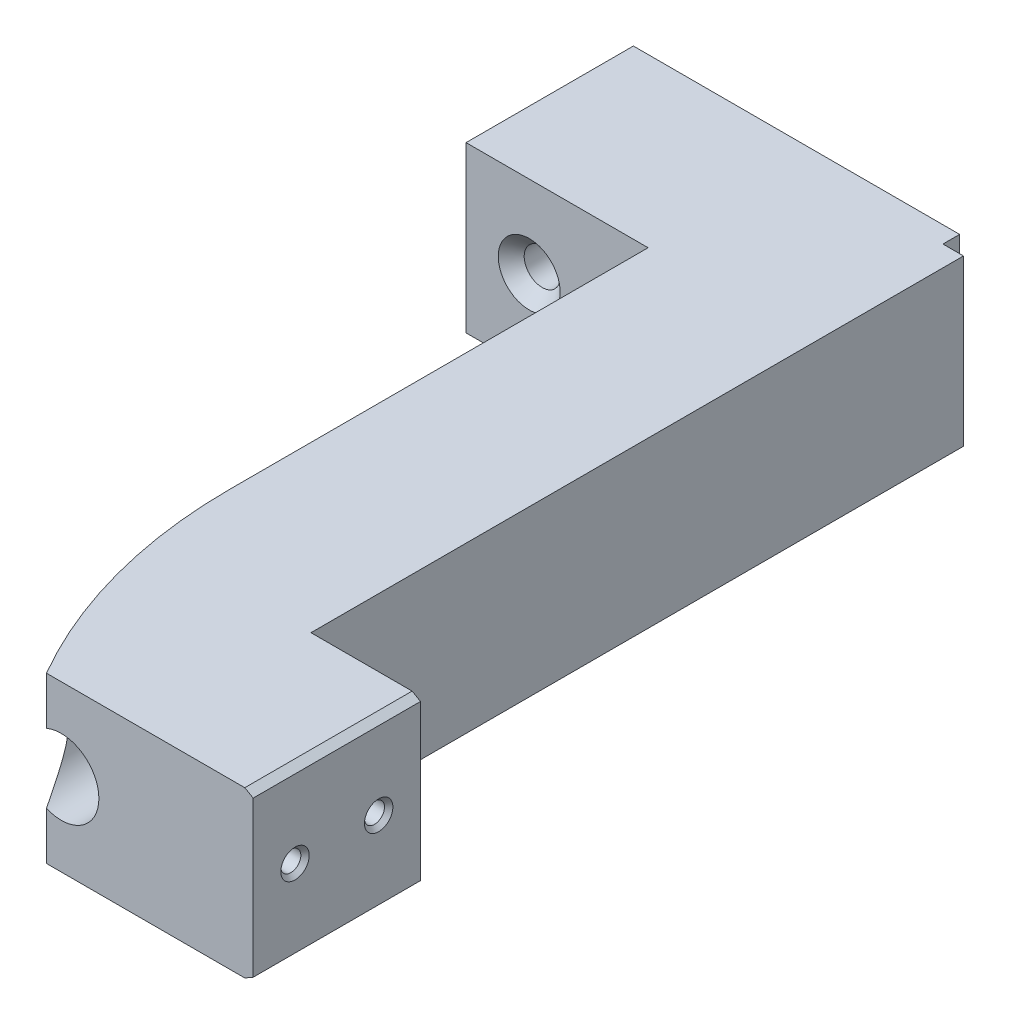
SolidWorks part; units mm, degrees
material "A286, generico"
ref_plane "Front" through (0, 0, 0) normal (0, 0, 1) x (1, 0, 0)
ref_plane "Top" through (0, 0, 0) normal (0, 1, 0) x (1, 0, 0)
ref_plane "Right" through (0, 0, 0) normal (1, 0, 0) x (0, 0, -1)
sketch "Schizzo1" plane through (0, 0, 0) normal (0, 0, 1) x (1, 0, 0)
  line L1 (0, 0) -> (39, 0)
  line L2 (0, 0) -> (0, 19.7)
  line L3 (0, 19.7) -> (39, 19.7)
  line L4 (39, 0) -> (39, 19.7)
extrude "Estrusione-Estrusione1" add sketch "Schizzo1" along normal blind 20
sketch "Schizzo2" plane through (0, 0, 20) normal (0, 0, 1) x (1, 0, 0)
  line L0 (0, 9.85) -> (7.55, 9.85)
  line L1 (0, 19.7) -> (0, 0) construction
  line L2 (7.55, 9.85) -> (31.6131, 9.85)
  line L3 (31.6131, 9.85) -> (39, 9.85)
  line L4 (39, 0) -> (39, 19.7) construction
  line L5 (39, 19.7) -> (0, 19.7) construction
  line L6 (41.4631, 0) -> (21.7631, 0)
  line L7 (41.4631, 0) -> (41.4631, 19.7)
  line L8 (41.4631, 19.7) -> (21.7631, 19.7)
  line L9 (21.7631, 0) -> (21.7631, 19.7)
  line L10 (41.4631, 0) -> (21.7631, 19.7) construction
  line L11 (41.4631, 19.7) -> (21.7631, 0) construction
  circle A0 centre (31.6131, 9.85) radius 4.5
  line M4 (0, 0) -> (39, 0)
  line M5 (39, 0) -> (39, 19.7)
  line M6 (39, 19.7) -> (0, 19.7)
hole_wizard "Foro svasato per Vite M4-1" positions "Schizzo3D1" profile "Schizzo3" countersink size "M4" standard "Ansi Metric" end condition up to next
sketch3d "Schizzo3D1"
  point P0 (7.55, 9.85, 20)
  point P3 (31.6131, 9.85, 20)
sketch "Schizzo3" plane through (7.55, 9.85, 20) normal (1, 0, 0) x (0, -1, 0)
  line L0 (0, 0) -> (0, 20)
  line L1 (0, 20) -> (2.15, 20)
  line L2 (2.15, 20) -> (2.15, 1.55)
  line L3 (2.15, 1.55) -> (3.7, 0)
  line L5 (3.7, 0) -> (0, 0)
  line L6 (-2.15, 1.55) -> (-3.7, 0) construction
  line L11 (0, -6.35) -> (0, 107.95) construction
  dimension "Thru Hole Dia." = 4.3
  dimension "Thru Hole Depth" = 20
  dimension "Near C'Sink Dia." = 7.4
  dimension "Near C'Sink Angle" = 90
extrude "Estrusione-Estrusione4" add sketch "Schizzo2" along normal blind 80 contours A0 L3 L9 L2 M5 M6 | A0 L2 L9 L3 M4 M5 | L7 L8 L6 M5
sketch "Schizzo7" plane through (0, 0, 20) normal (0, 0, -1) x (-1, 0, 0)
  line L1 (-39, 19.7) -> (-41.4631, 19.7)
  line L2 (-39, 19.7) -> (-39, 0)
  line L3 (-39, 0) -> (-41.4631, 0)
  line L4 (-41.4631, 19.7) -> (-41.4631, 0)
extrude "Estrusione-Estrusione5" add sketch "Schizzo7" along normal blind 18
sketch "Schizzo9" plane through (0, 19.7, 0) normal (0, 1, 0) x (1, 0, 0)
  line L3 (21.7631, -100) -> (21.7631, -20) construction
  line L4 (41.4631, -100) -> (21.7631, -100) construction
  line L5 (21.7631, -70) -> (21.7631, -100)
  line L6 (21.7631, -100) -> (29.8483, -100)
  arc A0 (21.7631, -70) -> (29.8483, -100) centre (81.4631, -70) ccw
extrude "Taglio-Estrusione2" cut sketch "Schizzo9" against normal through all
sketch "Schizzo10" plane through (41.4631, 0, 0) normal (1, 0, 0) x (0, 0, -1)
  line L0 (-100, 19.7) -> (-2, 19.7) construction
  line L2 (-100, 0) -> (-80, 0)
  line L3 (-100, 0) -> (-100, 19.7)
  line L4 (-100, 19.7) -> (-80, 19.7)
  line L5 (-80, 0) -> (-80, 19.7)
sketch "Schizzo11" plane through (0, 0, 2) normal (0, 0, -1) x (-1, 0, 0)
  line L0 (-39, 19.7) -> (-54.55, 19.7)
sketch "Schizzo14" plane through (0, 19.7, 0) normal (0, 1, 0) x (1, 0, 0)
  line L1 (39, -2) -> (54.55, -2)
  line L2 (39, -2) -> (39, -80)
  line L3 (39, -80) -> (54.55, -80)
  line L4 (54.55, -2) -> (54.55, -80)
sketch "Schizzo16" plane through (0, 19.7, 0) normal (0, 1, 0) x (1, 0, 0)
  line L0 (41.4631, -80) -> (54.55, -80)
  line L1 (41.4631, -100) -> (41.4631, -80) construction
sketch "Schizzo17" plane through (41.4631, 0, 0) normal (1, 0, 0) x (0, 0, -1)
  line L1 (-100, 19.7) -> (-80, 19.7)
  line L2 (-100, 19.7) -> (-100, 0)
  line L3 (-100, 0) -> (-80, 0)
  line L4 (-80, 19.7) -> (-80, 0)
  line L5 (-100, 19.7) -> (-80, 0) construction
  line L6 (-100, 0) -> (-80, 19.7) construction
  point P4 (-90, 9.85)
extrude "Estrusione-Estrusione7" add sketch "Schizzo17" along normal blind 13.09
chamfer "Smusso1" distance 1 angle 30 2 edges at (54.5531, 0, 90) (54.5531, 19.7, 90)
sketch "Schizzo18" plane through (54.5531, 0, 0) normal (1, 0, 0) x (0, 0, -1)
  line L0 (-100, 9.85) -> (-95, 9.85)
  line L1 (-100, 19.1226) -> (-100, 0.5774) construction
  line L2 (-95, 9.85) -> (-85, 9.85)
  line L3 (-85, 9.85) -> (-80, 9.85)
  line L4 (-80, 0.5774) -> (-80, 19.1226) construction
hole_wizard "Foro svasato per Vite M2-1" positions "Schizzo3D2" profile "Schizzo20" countersink size "M2" standard "Ansi Metric"
sketch3d "Schizzo3D2"
  point P0 (54.5531, 9.85, 95)
  point P3 (54.5531, 9.85, 85)
sketch "Schizzo20" plane through (54.5531, 9.85, 95) normal (0, 1, 0) x (0, 0, -1)
  line L0 (0, 0) -> (0, 5.721)
  line L1 (0, 5.721) -> (1.2, 5)
  line L2 (1.2, 5) -> (1.2, 0.5)
  line L3 (1.2, 0.5) -> (1.7, 0)
  line L5 (1.7, 0) -> (0, 0)
  line L6 (-1.2, 0.5) -> (-1.7, 0) construction
  line L10 (0, 5.721) -> (-1.2, 5) construction
  line L11 (0, -6.35) -> (0, 107.95) construction
  dimension "Hole Dia." = 2.4
  dimension "Hole Depth" = 5
  dimension "Near C'Sink Dia." = 3.4
  dimension "Near C'Sink Angle" = 90
  dimension "Drill Angle" = 118
sketch "Schizzo21" plane through (54.5531, 0, 0) normal (1, 0, 0) x (0, 0, -1)
  line L1 (-100, 19.1226) -> (-80, 19.1226)
  line L2 (-100, 19.1226) -> (-100, 0.5774)
  line L3 (-100, 0.5774) -> (-80, 0.5774)
  line L4 (-80, 19.1226) -> (-80, 0.5774)
  line L5 (-100, 19.1226) -> (-80, 0.5774) construction
  line L6 (-100, 0.5774) -> (-80, 19.1226) construction
  point P4 (-90, 9.85)
